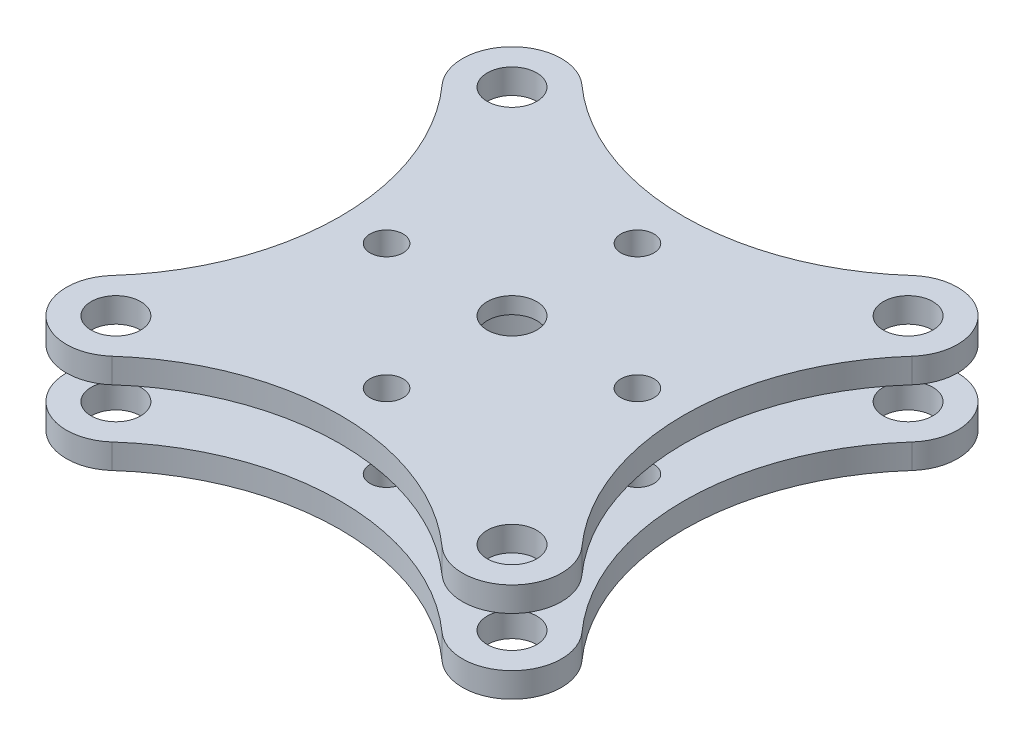
SolidWorks part; units mm, degrees
ref_plane "Front Plane" through (0, 0, 0) normal (0, 0, 1) x (1, 0, 0)
ref_plane "Top Plane" through (0, 0, 0) normal (0, 1, 0) x (1, 0, 0)
ref_plane "Right Plane" through (0, 0, 0) normal (1, 0, 0) x (0, 0, -1)
sketch "Sketch1" plane through (0, 0, 0) normal (0, 1, 0) x (1, 0, 0)
  line L0 (-137.1097, 0) -> (122.8067, 0) construction
  line L5 (-70.6066, -79.3934) -> (65.6991, 73.8752) construction
  line L6 (-70.6066, 70.6066) -> (70.6066, -70.6066) construction
  line L7 (0, 99.6844) -> (0, -90.5575) construction
  arc A0 (-50, 71.1803) -> (-71.1803, 50) centre (-60, 60) ccw
  circle A1 centre (0, 0) radius 27.5
  arc A2 (50, 71.1803) -> (71.1803, 50) centre (60, 60) cw
  arc A3 (50, -71.1803) -> (71.1803, -50) centre (60, -60) ccw
  arc A4 (-50, -71.1803) -> (-71.1803, -50) centre (-60, -60) cw
  arc A5 (-50, 71.1803) -> (50, 71.1803) centre (0, 127.082) ccw
  arc A6 (-50, -71.1803) -> (50, -71.1803) centre (0, -127.082) cw
  arc A7 (-71.1803, -50) -> (-71.1803, 50) centre (-127.082, 0) ccw
  arc A8 (71.1803, -50) -> (71.1803, 50) centre (127.082, 0) cw
  circle A9 centre (-60, 60) radius 7.5
  circle A10 centre (60, 60) radius 7.5
  circle A11 centre (-60, -60) radius 7.5
  circle A12 centre (60, -60) radius 7.5
  circle A13 centre (0, 38) radius 5
  circle A14 centre (-38, 0) radius 5
  circle A15 centre (0, -38) radius 5
  circle A16 centre (38, 0) radius 5
  point P0 (0, 0)
  dimension "D2" = 55
  dimension "D4" = 30
  dimension "D5" = 150
  dimension "D6" = 150
  dimension "D1" = 15
  dimension "D7" = 10
  dimension "D9" = 10
  dimension "D3" = 150
  dimension "D8" = 38
  dimension "D10" = 38
extrude "Boss-Extrude1" add sketch "Sketch1" against normal blind 7.5
sketch "Sketch2" plane through (0, 0, 0) normal (0, 1, 0) x (1, 0, 0)
  circle A0 centre (0, 0) radius 27.5 construction
  circle A1 centre (0, 0) radius 27.5
extrude "Boss-Extrude2" add sketch "Sketch2" against normal blind 30
ref_plane "Plane1" through (0, -15, 0) normal (0, 1, 0) x (1, 0, 0)
sketch "Sketch3" plane through (0, -30, 0) normal (0, -1, 0) x (1, 0, 0)
  circle A0 centre (0, 0) radius 25.5
  dimension "D1" = 51
extrude "Cut-Extrude1" cut sketch "Sketch3" against normal blind 25
sketch "Sketch4" plane through (0, -5, 0) normal (0, -1, 0) x (1, 0, 0)
  circle A0 centre (0, 0) radius 7.5
  dimension "D1" = 15
extrude "Cut-Extrude2" cut sketch "Sketch4" against normal blind 25
mirror "Mirror1" about plane through (0, -15, 0) normal (0, 1, 0) of "Boss-Extrude1"
